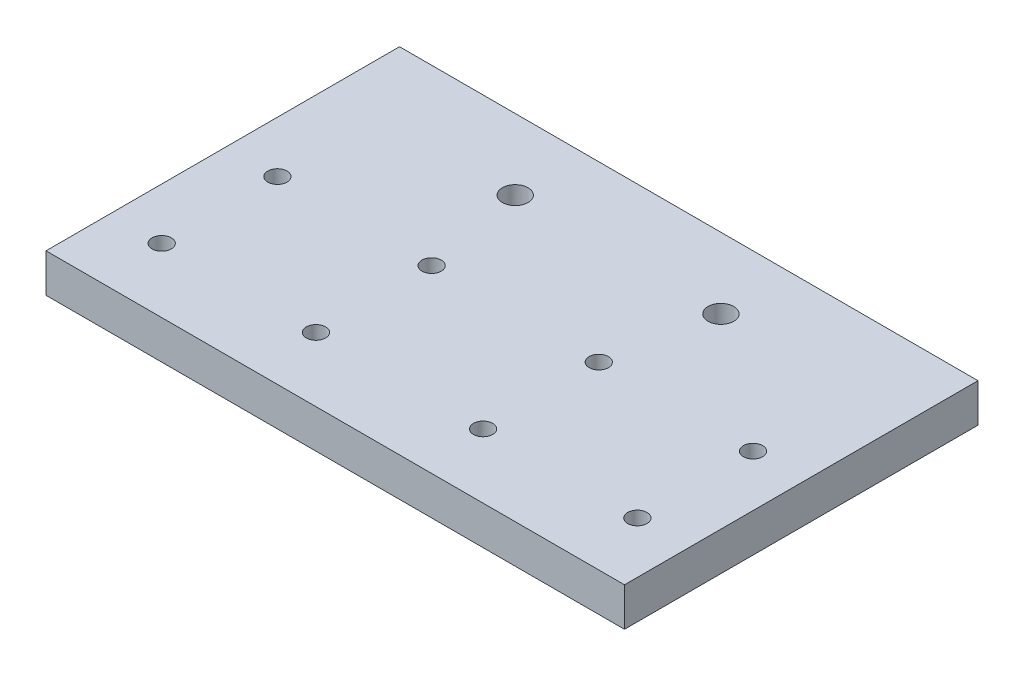
SolidWorks part; units mm, degrees
material "Acrylic (Medium-high impact)"
ref_plane "Front Plane" through (0, 0, 0) normal (0, 0, 1) x (1, 0, 0)
ref_plane "Top Plane" through (0, 0, 0) normal (0, 1, 0) x (1, 0, 0)
ref_plane "Right Plane" through (0, 0, 0) normal (1, 0, 0) x (0, 0, -1)
sketch "Sketch1" plane through (0, 0, 0) normal (0, 1, 0) x (1, 0, 0)
  line L0 (0, -383.892) -> (0, 18810.7071) construction
  line L1 (-45, 30) -> (45, 30)
  line L2 (-45, 30) -> (-45, -25)
  line L3 (-45, -25) -> (45, -25)
  line L4 (45, 30) -> (45, -25)
  line L7 (-383.892, 0) -> (18810.7071, 0) construction
  line L14 (25, -383.892) -> (25, 18810.7071) construction
  line L16 (13, -15) -> (37, -15) construction
  line L18 (13, -15) -> (13, 3) construction
  line L19 (13, 3) -> (37, 3) construction
  line L20 (37, -15) -> (37, 3) construction
  line L21 (13, -15) -> (37, 3) construction
  line L22 (13, 3) -> (37, -15) construction
  circle A2 centre (37, 3) radius 1.5
  circle A3 centre (13, 3) radius 1.5
  circle A4 centre (37, -15) radius 1.5
  circle A5 centre (13, -15) radius 1.5
  circle A6 centre (-37, -15) radius 1.5
  circle A7 centre (-37, 3) radius 1.5
  circle A8 centre (-13, -15) radius 1.5
  circle A9 centre (-13, 3) radius 1.5
  point P0 (0, 0)
  point P19 (25, -6)
  dimension "D13" = 3
  dimension "D15" = 18
  dimension "D2" = 90
  dimension "D3" = 30
  dimension "D4" = 25
  dimension "D5" = 45
  dimension "D10" = 24
  dimension "D11" = 18
  dimension "D12" = 10
  dimension "D9" = 25
  dimension "D14" = 2
extrude "Boss-Extrude1" add sketch "Sketch1" along normal blind 6
sketch "Sketch2" plane through (0, 6, 0) normal (0, 1, 0) x (1, 0, 0)
  line L0 (45, -25) -> (45, 30) construction
  line L3 (0, -1000) -> (0, 49000) construction
  line L4 (45, 30) -> (-45, 30) construction
  circle A0 centre (16, 19) radius 2
  circle A3 centre (-16, 19) radius 2
  dimension "D1" = 11
  dimension "D2" = 4
  dimension "D3" = 29
extrude "Cut-Extrude1" cut sketch "Sketch2" against normal up to next
